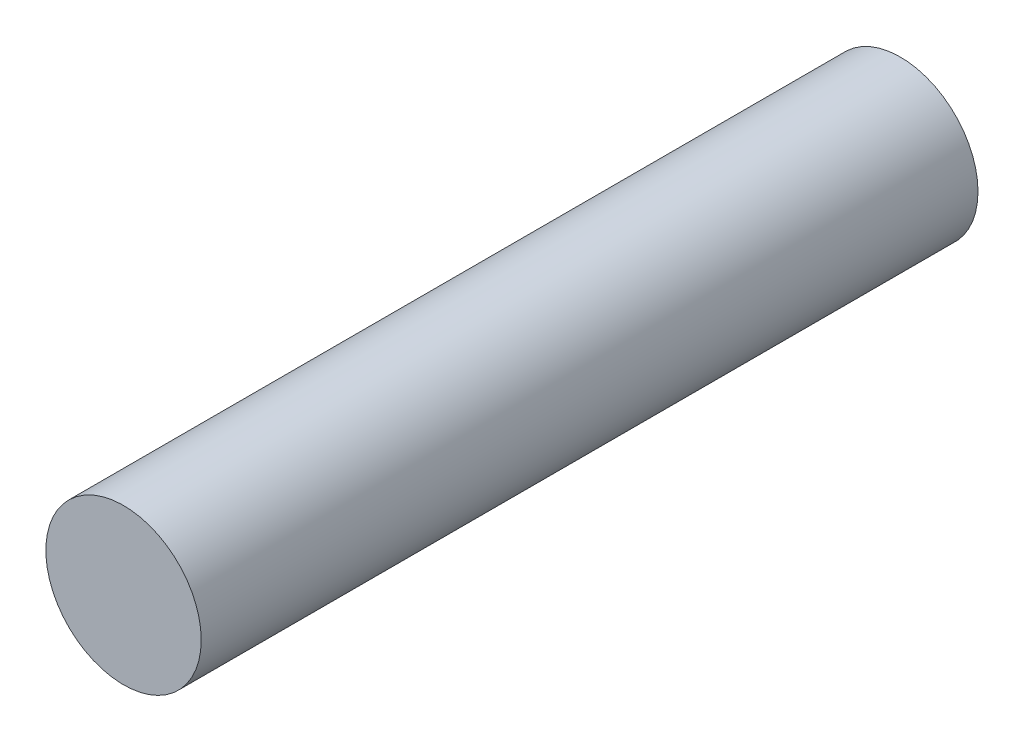
SolidWorks part; units mm, degrees
ref_plane "Front Plane" through (0, 0, 0) normal (0, 0, 1) x (1, 0, 0)
ref_plane "Top Plane" through (0, 0, 0) normal (0, 1, 0) x (1, 0, 0)
ref_plane "Right Plane" through (0, 0, 0) normal (1, 0, 0) x (0, 0, -1)
sketch "Sketch1" plane through (0, 0, 0) normal (0, 0, 1) x (1, 0, 0)
  circle A0 centre (0, 0) radius 6.35
  dimension "D1" = 12.7
extrude "Boss-Extrude1" add sketch "Sketch1" along normal mid plane 63.5
